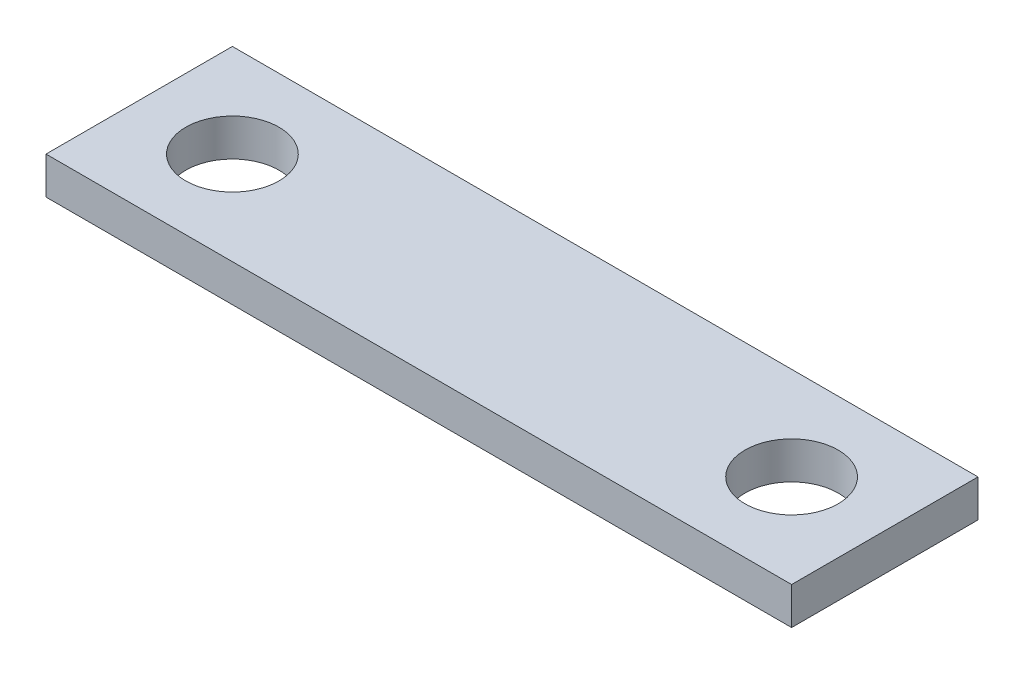
SolidWorks part; units mm, degrees
ref_plane "Front Plane" through (0, 0, 0) normal (0, 0, 1) x (1, 0, 0)
ref_plane "Top Plane" through (0, 0, 0) normal (0, 1, 0) x (1, 0, 0)
ref_plane "Right Plane" through (0, 0, 0) normal (1, 0, 0) x (0, 0, -1)
sketch "Sketch1" plane through (0, 0, 0) normal (0, 1, 0) x (1, 0, 0)
  line L0 (0, 2.5) -> (0, -2.5) construction
  line L1 (-10, 2.5) -> (10, 2.5)
  line L2 (-10, 2.5) -> (-10, -2.5)
  line L3 (-10, -2.5) -> (10, -2.5)
  line L4 (10, 2.5) -> (10, -2.5)
  line L5 (-10, 2.5) -> (10, -2.5) construction
  line L6 (-10, -2.5) -> (10, 2.5) construction
  circle A0 centre (-7.5, 0) radius 1.25
  circle A1 centre (7.5, 0) radius 1.25
  point P0 (0, 0)
  dimension "D3" = 2.5
  dimension "D4" = 2.5
  dimension "D1" = 5
  dimension "D2" = 20
extrude "Boss-Extrude1" add sketch "Sketch1" along normal blind 1
